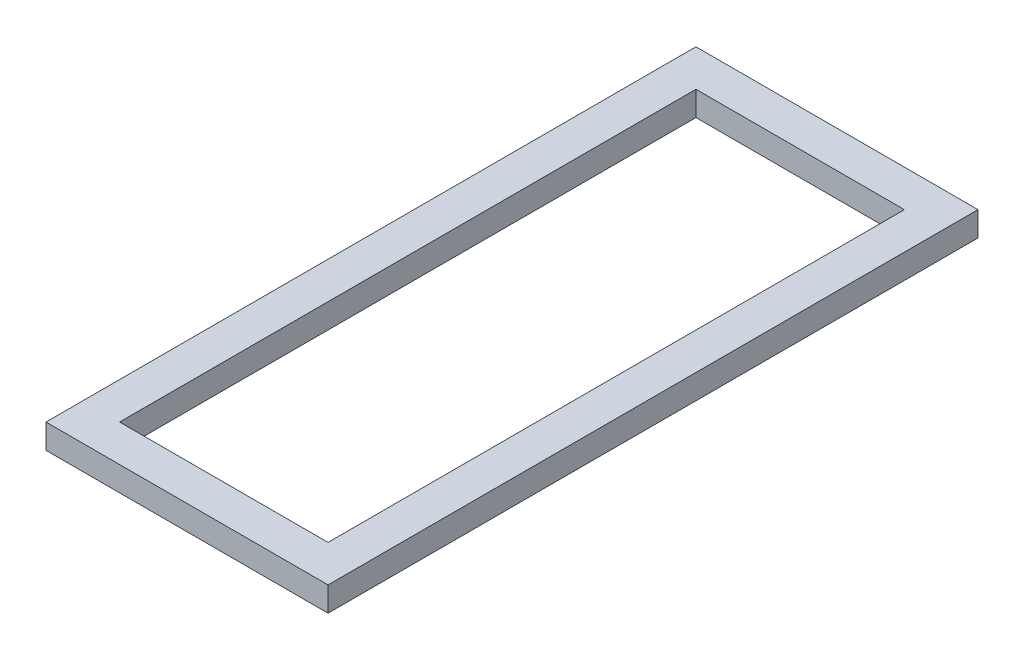
SolidWorks part; units mm, degrees
ref_plane "Front Plane" through (0, 0, 0) normal (0, 0, 1) x (1, 0, 0)
ref_plane "Top Plane" through (0, 0, 0) normal (0, 1, 0) x (1, 0, 0)
ref_plane "Right Plane" through (0, 0, 0) normal (1, 0, 0) x (0, 0, -1)
sketch "Sketch1" plane through (0, 0, 0) normal (0, 1, 0) x (1, 0, 0)
  line L1 (-94.0639, 363.9269) -> (105.9361, 363.9269)
  line L2 (-94.0639, 363.9269) -> (-94.0639, -136.0731)
  line L3 (-94.0639, -136.0731) -> (105.9361, -136.0731)
  line L4 (105.9361, 363.9269) -> (105.9361, -136.0731)
  dimension "D1" = 200
  dimension "D2" = 500
extrude "Extrude-Thin1" add sketch "Sketch1" along normal blind 20 thin thin type mid plane wall 30
